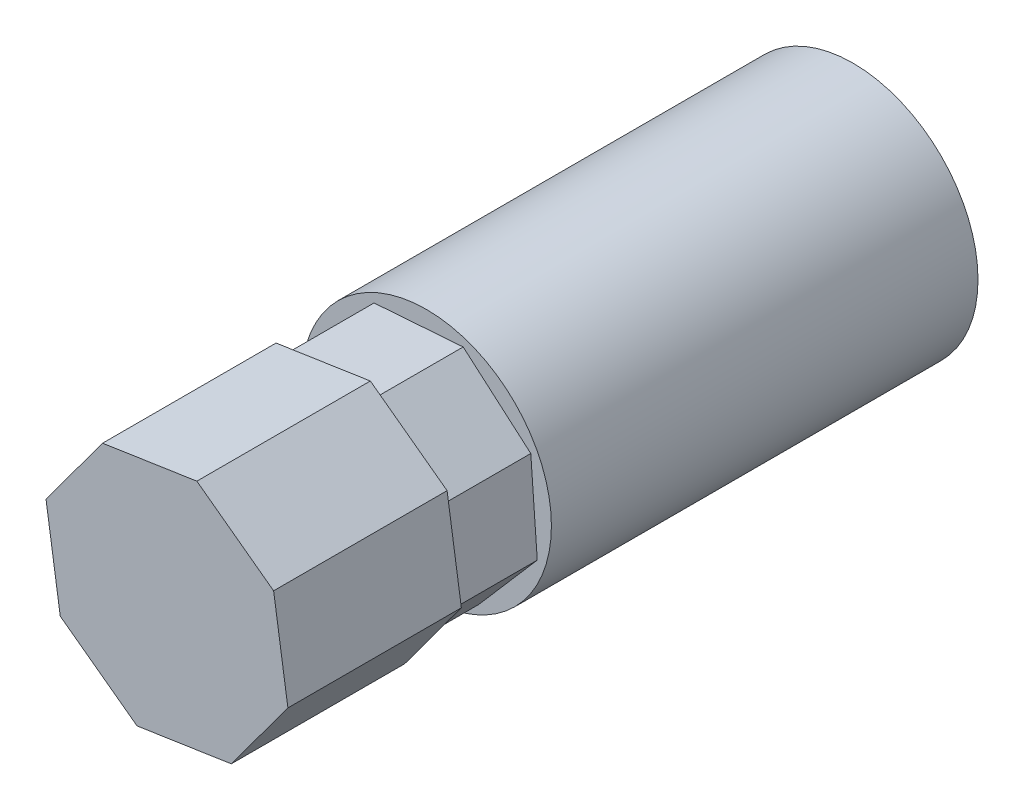
SolidWorks part; units mm, degrees
ref_plane "Front Plane" through (0, 0, 0) normal (0, 0, 1) x (1, 0, 0)
ref_plane "Top Plane" through (0, 0, 0) normal (0, 1, 0) x (1, 0, 0)
ref_plane "Right Plane" through (0, 0, 0) normal (1, 0, 0) x (0, 0, -1)
sketch "Sketch1" plane through (0, 0, 0) normal (0, 0, 1) x (1, 0, 0)
  circle A0 centre (0, 0) radius 3.1115
  circle A1 centre (0, 0) radius 4.5022
  dimension "D1" = 6.223
  dimension "D2" = 9.0043
extrude "Boss-Extrude2" add sketch "Sketch1" along normal blind 15.367
sketch "Sketch2" plane through (0, 0, 15.367) normal (0, 0, 1) x (1, 0, 0)
  line L0 (3.7594, 1.8869) -> (1.3241, 3.9926)
  line L1 (-1.8869, 3.7594) -> (-3.9926, 1.3241)
  line L2 (-3.9926, 1.3241) -> (-3.7594, -1.8869)
  line L3 (-3.7594, -1.8869) -> (-1.3241, -3.9926)
  line L4 (-1.3241, -3.9926) -> (1.8869, -3.7594)
  line L5 (1.8869, -3.7594) -> (3.9926, -1.3241)
  line L6 (3.9926, -1.3241) -> (3.7594, 1.8869)
  line L7 (1.3241, 3.9926) -> (-1.8869, 3.7594)
  circle A0 centre (0, 0) radius 3.8862 construction
  point P1 (-2.5417, -2.9397)
  dimension "D1" = 7.7724
extrude "Boss-Extrude3" add sketch "Sketch2" along normal blind 3.0988
sketch "Sketch3" plane through (0, 0, 18.4658) normal (0, 0, 1) x (1, 0, 0)
  line L1 (-2.3184, 3.843) -> (-4.3568, 1.078)
  line L2 (-4.3568, 1.078) -> (-3.843, -2.3184)
  line L3 (-3.843, -2.3184) -> (-1.078, -4.3568)
  line L4 (-1.078, -4.3568) -> (2.3184, -3.843)
  line L5 (2.3184, -3.843) -> (4.3568, -1.078)
  line L6 (4.3568, -1.078) -> (3.843, 2.3184)
  line L7 (3.843, 2.3184) -> (1.078, 4.3568)
  line L8 (1.078, 4.3568) -> (-2.3184, 3.843)
  circle A0 centre (0, 0) radius 4.1465 construction
  dimension "D1" = 8.2931
extrude "Boss-Extrude4" add sketch "Sketch3" along normal blind 6.2484
